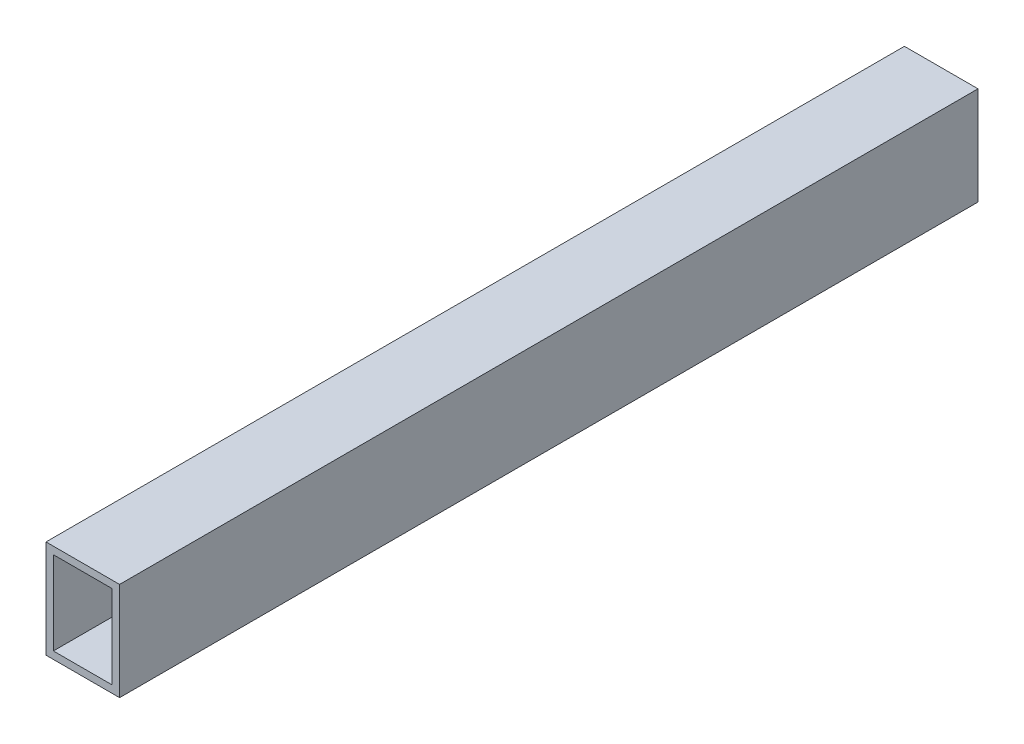
SolidWorks part; units mm, degrees
ref_plane "Front Plane" through (0, 0, 0) normal (0, 0, 1) x (1, 0, 0)
ref_plane "Top Plane" through (0, 0, 0) normal (0, 1, 0) x (1, 0, 0)
ref_plane "Right Plane" through (0, 0, 0) normal (1, 0, 0) x (0, 0, -1)
sketch "Croquis1" plane through (0, 0, 0) normal (1, 0, 0) x (0, 0, -1)
  line L0 (-175, -20) -> (-175, 20)
  line L1 (-175, -20) -> (175, -20)
  line L2 (-175, 20) -> (175, 20)
  line L3 (175, -20) -> (175, 20)
  line L4 (-175, -20) -> (175, 20) construction
  line L5 (-175, 20) -> (175, -20) construction
  point P1 (0, 0)
  dimension "D1" = 350
  dimension "D2" = 40
extrude "Saliente-Extruir1" add sketch "Croquis1" along normal blind 30
sketch "Croquis2" plane through (0, 0, 175) normal (0, 0, 1) x (1, 0, 0)
  line L0 (3, -17) -> (27, -17)
  line L1 (3, -17) -> (3, 17)
  line L2 (27, -17) -> (27, 17)
  line L3 (3, 17) -> (27, 17)
  line L4 (3, -17) -> (27, 17) construction
  line L5 (27, -17) -> (3, 17) construction
  line L6 (30, 20) -> (30, -20) construction
  line L7 (30, 20) -> (0, 20) construction
  line L8 (0, 20) -> (0, -20) construction
  line L9 (30, -20) -> (0, -20) construction
  point P1 (15, 0)
  dimension "D1" = 3
  dimension "D2" = 3
  dimension "D3" = 3
  dimension "D4" = 3
extrude "Cortar-Extruir1" cut sketch "Croquis2" against normal blind 890
